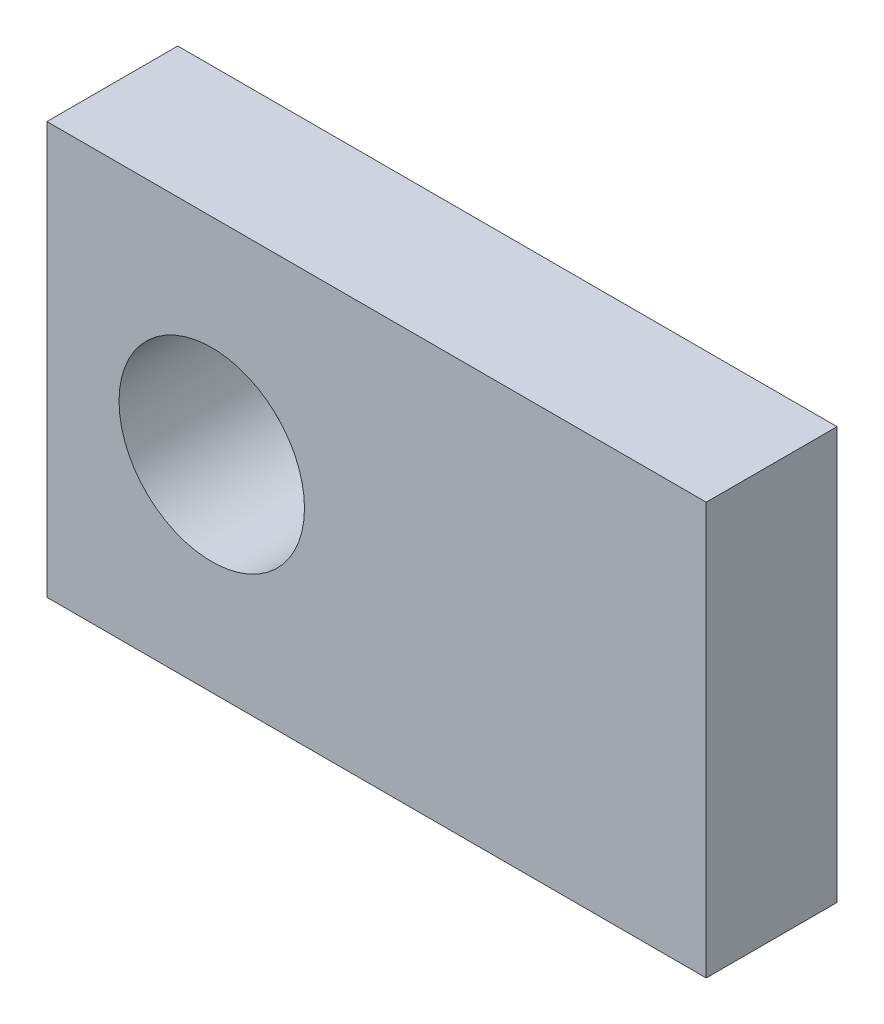
SolidWorks part; units mm, degrees
ref_plane "Front Plane" through (0, 0, 0) normal (0, 0, 1) x (1, 0, 0)
ref_plane "Top Plane" through (0, 0, 0) normal (0, 1, 0) x (1, 0, 0)
ref_plane "Right Plane" through (0, 0, 0) normal (1, 0, 0) x (0, 0, -1)
sketch "Sketch1" plane through (0, 0, 0) normal (0, 0, 1) x (1, 0, 0)
  line L1 (8, -5) -> (-8, -5)
  line L2 (8, -5) -> (8, 5)
  line L3 (8, 5) -> (-8, 5)
  line L4 (-8, -5) -> (-8, 5)
  line L5 (8, -5) -> (-8, 5) construction
  line L6 (8, 5) -> (-8, -5) construction
  point P0 (0, 0)
  dimension "D1" = 16
  dimension "D2" = 10
extrude "Boss-Extrude1" add sketch "Sketch1" along normal mid plane 3.175
sketch "Sketch4" plane through (0, 0, 1.5875) normal (0, 0, 1) x (1, 0, 0)
  line L0 (-8, 5) -> (-8, -5) construction
  point P0 (-4, 0)
  point P3 (0, 0)
  dimension "D1" = 4
hole_wizard "M4 Clearance Hole1" positions "Sketch4" profile "Sketch3" hole size "M4" standard "ANSI Metric" end condition through all
sketch "Sketch3" plane through (-4, 0, 1.5875) normal (1, 0, 0) x (0, -1, 0)
  line L0 (0, 0) -> (0, 3.175)
  line L1 (0, 3.175) -> (2.25, 3.175)
  line L2 (2.25, 3.175) -> (2.25, 0)
  line L5 (2.25, 0) -> (0, 0)
  line L11 (0, -6.35) -> (0, 107.95) construction
  dimension "Thru Hole Dia." = 4.5
  dimension "Thru Hole Depth" = 3.175
